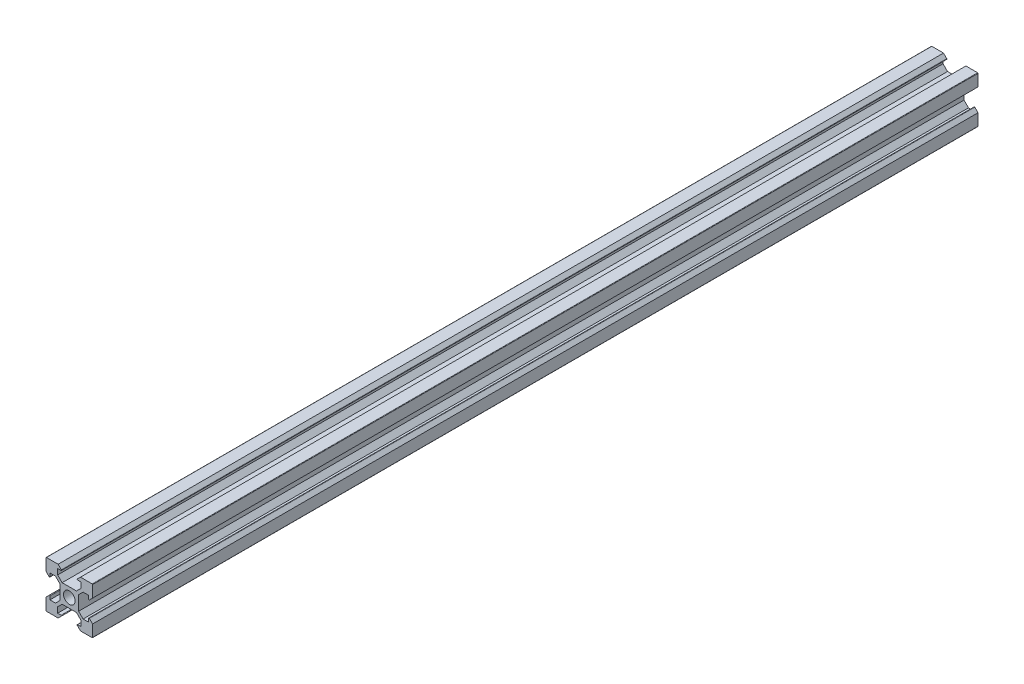
SolidWorks part; units mm, degrees
ref_plane "Front Plane" through (0, 0, 0) normal (0, 0, 1) x (1, 0, 0)
ref_plane "Top Plane" through (0, 0, 0) normal (0, 1, 0) x (1, 0, 0)
ref_plane "Right Plane" through (0, 0, 0) normal (1, 0, 0) x (0, 0, -1)
sketch "Sketch1" plane through (0, 0, 0) normal (0, 0, 1) x (1, 0, 0)
  line L0 (-10, 9.8109) -> (-10, 4.8)
  line L1 (-10, -10) -> (10, -10) construction
  line L2 (-10, -10) -> (-10, 10) construction
  line L3 (-10, 10) -> (10, 10) construction
  line L4 (10, -10) -> (10, 10) construction
  line L5 (-10, -10) -> (10, 10) construction
  line L6 (-10, 10) -> (10, -10) construction
  line L7 (-10, 4.8) -> (-8.6228, 3.4228)
  line L8 (-8.3, 3.5565) -> (-8.3, 5)
  line L9 (-8.3, 5) -> (-5.9192, 5)
  line L10 (-5.9192, 5) -> (-4, 3.0808)
  line L11 (-4, 3.0808) -> (-4, -3.0808)
  line L12 (-9.8109, 10) -> (-4.8, 10)
  line L13 (-3.5565, 8.3) -> (-5, 8.3)
  line L14 (-4.8, 10) -> (-3.4228, 8.6228)
  line L15 (-5, 8.3) -> (-5, 5.9192)
  line L16 (-5, 5.9192) -> (-3.0808, 4)
  line L17 (-3.0808, 4) -> (3.0808, 4)
  line L18 (4, -3.0808) -> (4, 3.0808)
  line L19 (5.9192, -5) -> (4, -3.0808)
  line L20 (8.3, -5) -> (5.9192, -5)
  line L21 (8.3, -3.5565) -> (8.3, -5)
  line L22 (10, -4.8) -> (8.6228, -3.4228)
  line L23 (10, -9.8109) -> (10, -4.8)
  line L24 (9.8109, -10) -> (4.8, -10)
  line L25 (4.8, -10) -> (3.4228, -8.6228)
  line L26 (3.5565, -8.3) -> (5, -8.3)
  line L27 (5, -8.3) -> (5, -5.9192)
  line L28 (5, -5.9192) -> (3.0808, -4)
  line L29 (3.0808, -4) -> (0, -4)
  line L30 (-10, 0) -> (10, 0) construction
  line L31 (-10, -9.8109) -> (-10, -4.8)
  line L32 (-5.9192, -5) -> (-4, -3.0808)
  line L33 (-8.3, -5) -> (-5.9192, -5)
  line L34 (-8.3, -3.5565) -> (-8.3, -5)
  line L35 (-10, -4.8) -> (-8.6228, -3.4228)
  line L36 (0, 10) -> (0, -10) construction
  line L37 (9.8109, 10) -> (4.8, 10)
  line L38 (4.8, 10) -> (3.4228, 8.6228)
  line L39 (3.5565, 8.3) -> (5, 8.3)
  line L40 (5, 8.3) -> (5, 5.9192)
  line L41 (5, 5.9192) -> (3.0808, 4)
  line L42 (10, 9.8109) -> (10, 4.8)
  line L43 (10, 4.8) -> (8.6228, 3.4228)
  line L44 (8.3, 3.5565) -> (8.3, 5)
  line L45 (8.3, 5) -> (5.9192, 5)
  line L46 (5.9192, 5) -> (4, 3.0808)
  line L47 (-3.0808, -4) -> (0, -4)
  line L48 (-5, -5.9192) -> (-3.0808, -4)
  line L49 (-5, -8.3) -> (-5, -5.9192)
  line L50 (-3.5565, -8.3) -> (-5, -8.3)
  line L51 (-4.8, -10) -> (-3.4228, -8.6228)
  line L52 (-9.8109, -10) -> (-4.8, -10)
  circle A0 centre (0, 0) radius 2.5
  arc A1 (8.6228, 3.4228) -> (8.3, 3.5565) centre (8.4891, 3.5565) cw
  arc A2 (-10, 9.8109) -> (-9.8109, 10) centre (-9.8109, 9.8109) cw
  arc A3 (-8.6228, 3.4228) -> (-8.3, 3.5565) centre (-8.4891, 3.5565) ccw
  arc A4 (-3.5565, -8.3) -> (-3.4228, -8.6228) centre (-3.5565, -8.4891) cw
  arc A5 (-8.3, -3.5565) -> (-8.6228, -3.4228) centre (-8.4891, -3.5565) ccw
  arc A6 (-10, -9.8109) -> (-9.8109, -10) centre (-9.8109, -9.8109) ccw
  arc A7 (10, -9.8109) -> (9.8109, -10) centre (9.8109, -9.8109) cw
  arc A8 (3.4228, -8.6228) -> (3.5565, -8.3) centre (3.5565, -8.4891) cw
  arc A9 (8.3, -3.5565) -> (8.6228, -3.4228) centre (8.4891, -3.5565) cw
  arc A10 (9.8109, 10) -> (10, 9.8109) centre (9.8109, 9.8109) cw
  arc A11 (3.4228, 8.6228) -> (3.5565, 8.3) centre (3.5565, 8.4891) ccw
  arc A12 (-3.5565, 8.3) -> (-3.4228, 8.6228) centre (-3.5565, 8.4891) ccw
  point P39 (-4, 0)
  point P45 (0, 4)
  point P51 (4, 0)
  point P58 (8.3, 3.1)
  point P64 (-8.3, 3.1)
  point P67 (-3.1, -8.3)
  point P70 (-8.3, -3.1)
  point P79 (3.1, -8.3)
  point P82 (8.3, -3.1)
  point P88 (3.1, 8.3)
  point P91 (-3.1, 8.3)
  dimension "D1" = 5
  dimension "D8" = 0.1891
  dimension "D2" = 20
  dimension "D3" = 8
  dimension "D4" = 5
  dimension "D5" = 1.7
  dimension "D6" = 1.3
  dimension "D7" = 6.2
extrude "Boss-Extrude4" add sketch "Sketch1" along normal blind 380
